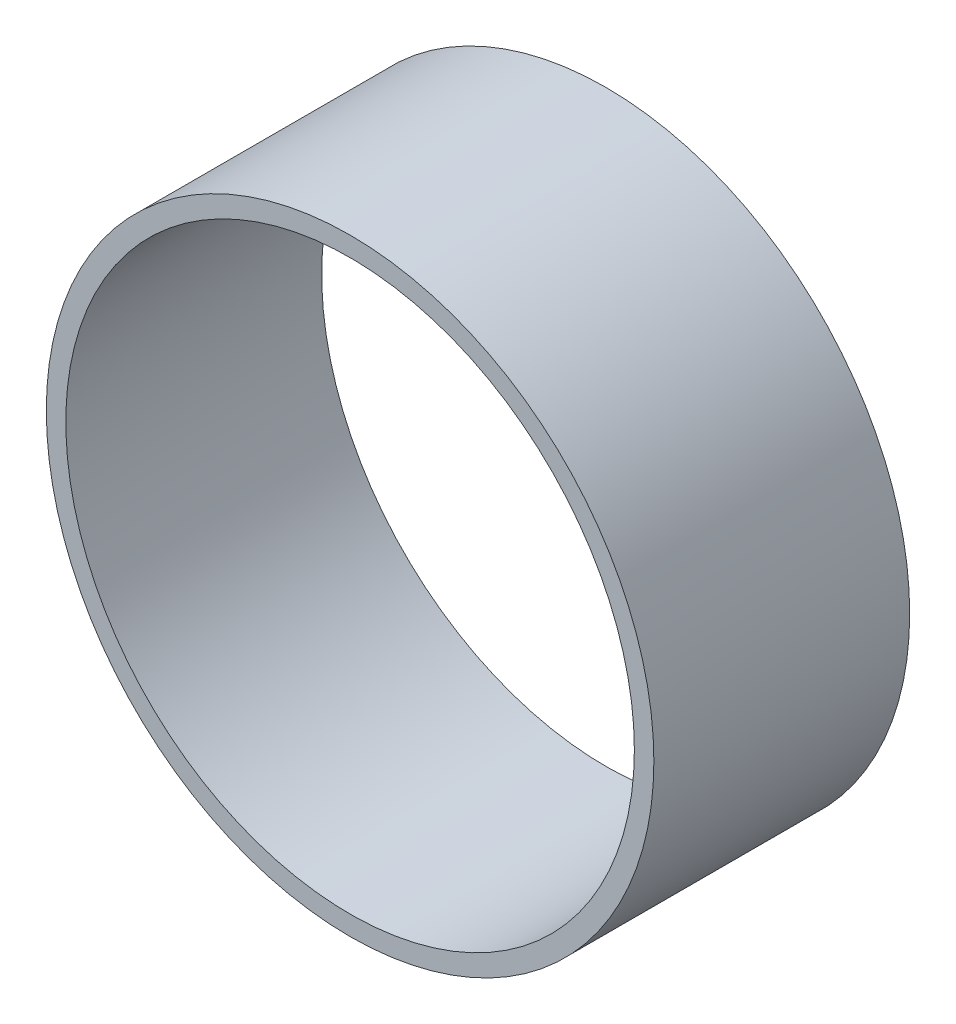
SolidWorks part; units mm, degrees
material "Plain Carbon Steel"
ref_plane "Front Plane" through (0, 0, 0) normal (0, 0, 1) x (1, 0, 0)
ref_plane "Top Plane" through (0, 0, 0) normal (0, 1, 0) x (1, 0, 0)
ref_plane "Right Plane" through (0, 0, 0) normal (1, 0, 0) x (0, 0, -1)
sketch "Sketch1" plane through (0, 0, 0) normal (0, 0, 1) x (1, 0, 0)
  circle A0 centre (0, 0) radius 23.75
  circle A1 centre (0, 0) radius 22.225
  dimension "D1" = 47.5
  dimension "D2" = 44.45
extrude "Boss-Extrude1" add sketch "Sketch1" along normal blind 20
